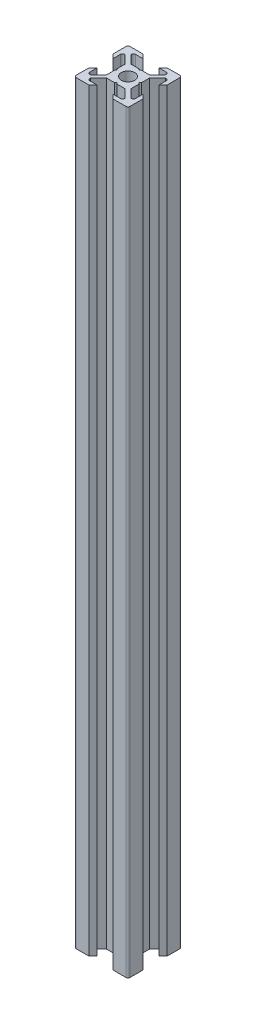
SolidWorks part; units mm, degrees
ref_plane "Face" through (0, 0, 0) normal (0, 0, 1) x (1, 0, 0)
ref_plane "Dessus" through (0, 0, 0) normal (0, 1, 0) x (1, 0, 0)
ref_plane "Droite" through (0, 0, 0) normal (1, 0, 0) x (0, 0, -1)
sketch "Esquisse1" plane through (0, 0, 0) normal (0, 1, 0) x (1, 0, 0)
  line L0 (0, 0) -> (0, 10) construction
  line L1 (0, 0) -> (-10, 0) construction
  line L2 (-10, 0) -> (-10, 10) construction
  line L3 (-10, 10) -> (0, 10) construction
  line L4 (0, 4) -> (-0.5, 4.5)
  line L5 (-0.5, 4.5) -> (-3.4393, 4.5)
  line L6 (-3.4393, 4.5) -> (-6.4393, 7.5)
  line L7 (-6.4393, 7.5) -> (-6.4393, 8.5)
  line L8 (-6.4393, 8.5) -> (-3, 8.5)
  line L9 (-3, 8.5) -> (-4.5, 10)
  line L10 (-4.5, 10) -> (-10, 10)
  line L11 (0, 0) -> (-10, 10) construction
  line L12 (-10, 4.5) -> (-10, 10)
  line L13 (-8.5, 3) -> (-10, 4.5)
  line L14 (-8.5, 6.4393) -> (-8.5, 3)
  line L15 (-7.5, 6.4393) -> (-8.5, 6.4393)
  line L16 (-4.5, 3.4393) -> (-7.5, 6.4393)
  line L17 (-4.5, 0.5) -> (-4.5, 3.4393)
  line L18 (-4, 0) -> (-4.5, 0.5)
  line L19 (0, -4) -> (-0.5, -4.5)
  line L20 (-0.5, -4.5) -> (-3.4393, -4.5)
  line L21 (-4, 0) -> (-4.5, -0.5)
  line L22 (-4.5, -0.5) -> (-4.5, -3.4393)
  line L23 (-4.5, -3.4393) -> (-7.5, -6.4393)
  line L24 (-3.4393, -4.5) -> (-6.4393, -7.5)
  line L25 (-3, -8.5) -> (-4.5, -10)
  line L26 (-6.4393, -8.5) -> (-3, -8.5)
  line L27 (-6.4393, -7.5) -> (-6.4393, -8.5)
  line L28 (-7.5, -6.4393) -> (-8.5, -6.4393)
  line L29 (-4.5, -10) -> (-10, -10)
  line L30 (-10, -4.5) -> (-10, -10)
  line L31 (-8.5, -3) -> (-10, -4.5)
  line L32 (-8.5, -6.4393) -> (-8.5, -3)
  line L33 (8.5, -6.4393) -> (8.5, -3)
  line L34 (8.5, -3) -> (10, -4.5)
  line L35 (10, -4.5) -> (10, -10)
  line L36 (4.5, -10) -> (10, -10)
  line L37 (7.5, -6.4393) -> (8.5, -6.4393)
  line L38 (6.4393, -7.5) -> (6.4393, -8.5)
  line L39 (6.4393, -8.5) -> (3, -8.5)
  line L40 (3, -8.5) -> (4.5, -10)
  line L41 (3.4393, -4.5) -> (6.4393, -7.5)
  line L42 (4.5, -3.4393) -> (7.5, -6.4393)
  line L43 (4.5, -0.5) -> (4.5, -3.4393)
  line L44 (4, 0) -> (4.5, -0.5)
  line L45 (0.5, -4.5) -> (3.4393, -4.5)
  line L46 (0, -4) -> (0.5, -4.5)
  line L47 (4, 0) -> (4.5, 0.5)
  line L48 (4.5, 0.5) -> (4.5, 3.4393)
  line L49 (4.5, 3.4393) -> (7.5, 6.4393)
  line L50 (7.5, 6.4393) -> (8.5, 6.4393)
  line L51 (8.5, 6.4393) -> (8.5, 3)
  line L52 (8.5, 3) -> (10, 4.5)
  line L53 (10, 4.5) -> (10, 10)
  line L54 (4.5, 10) -> (10, 10)
  line L55 (3, 8.5) -> (4.5, 10)
  line L56 (6.4393, 8.5) -> (3, 8.5)
  line L57 (6.4393, 7.5) -> (6.4393, 8.5)
  line L58 (3.4393, 4.5) -> (6.4393, 7.5)
  line L59 (0.5, 4.5) -> (3.4393, 4.5)
  line L60 (0, 4) -> (0.5, 4.5)
  circle A0 centre (0, 0) radius 2.5
  dimension "D10" = 5
  dimension "D1" = 10
  dimension "D2" = 45
  dimension "D3" = 45
  dimension "D4" = 1.5
  dimension "D5" = 7
  dimension "D6" = 1
  dimension "D7" = 4.5
  dimension "D8" = 0.5
  dimension "D9" = 0.75
extrude "Extrusion1" add sketch "Esquisse1" along normal blind 280
fillet "Congé1" radius 0.75 12 edges at (-8.5, 140, -6.4393) (-6.4393, 140, -8.5) (8.5, 140, -6.4393) (6.4393, 140, -8.5) (-8.5, 140, 6.4393) (-6.4393, 140, 8.5) (8.5, 140, 6.4393) (6.4393, 140, 8.5) (10, 140, -10) (-10, 140, -10) (-10, 140, 10) (10, 140, 10)
